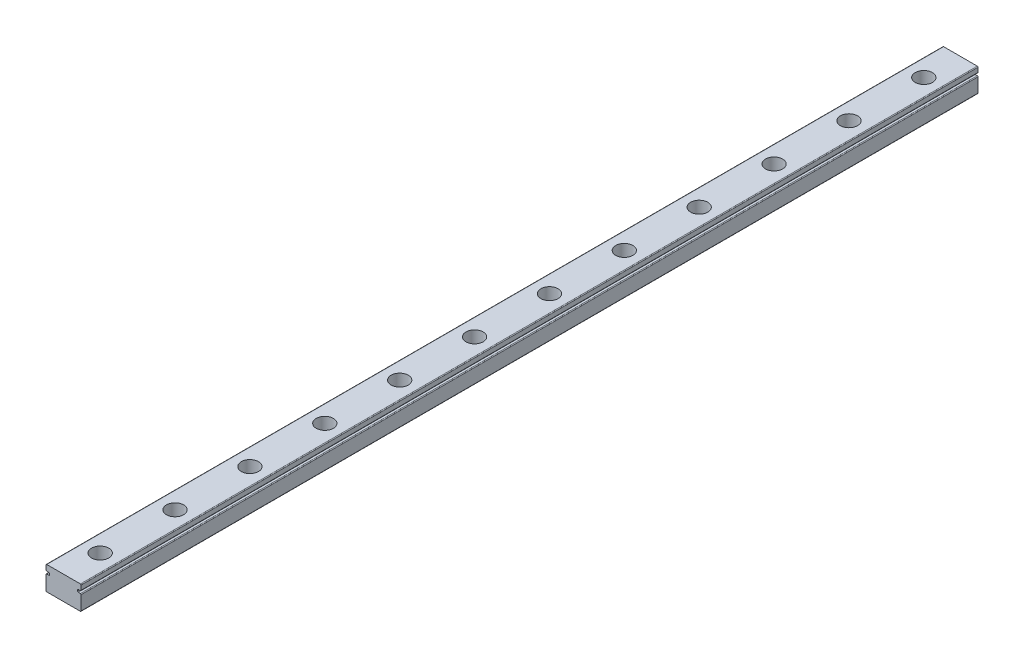
SolidWorks part; units mm, degrees
ref_plane "Front Plane" through (0, 0, 0) normal (0, 0, 1) x (1, 0, 0)
ref_plane "Top Plane" through (0, 0, 0) normal (0, 1, 0) x (1, 0, 0)
ref_plane "Right Plane" through (0, 0, 0) normal (1, 0, 0) x (0, 0, -1)
sketch "Sketch1" plane through (0, 0, 0) normal (0, 0, 1) x (1, 0, 0)
  line L0 (-5.715, 2.0574) -> (-5.0419, 2.0574)
  line L1 (-5.715, 4.0386) -> (5.715, 4.0386)
  line L2 (-5.969, 3.7846) -> (-5.969, 2.3114)
  line L3 (-5.715, -4.0386) -> (5.715, -4.0386)
  line L4 (5.969, 3.7846) -> (5.969, 2.3114)
  line L5 (-5.969, 4.0386) -> (5.969, -4.0386) construction
  line L6 (-5.969, -4.0386) -> (5.969, 4.0386) construction
  line L7 (-4.7879, 1.8034) -> (-4.7879, 1.4732)
  line L8 (-5.0419, 1.2192) -> (-5.715, 1.2192)
  line L9 (0, 4.0386) -> (0, -4.0386) construction
  line L10 (5.0419, 1.2192) -> (5.715, 1.2192)
  line L11 (4.7879, 1.8034) -> (4.7879, 1.4732)
  line L12 (5.715, 2.0574) -> (5.0419, 2.0574)
  line L13 (-5.969, 0.9652) -> (-5.969, -3.7846)
  line L14 (5.969, 0.9652) -> (5.969, -3.7846)
  arc A0 (5.715, -4.0386) -> (5.969, -3.7846) centre (5.715, -3.7846) ccw
  arc A1 (5.715, 1.2192) -> (5.969, 0.9652) centre (5.715, 0.9652) cw
  arc A2 (5.715, 4.0386) -> (5.969, 3.7846) centre (5.715, 3.7846) cw
  arc A3 (5.715, 2.0574) -> (5.969, 2.3114) centre (5.715, 2.3114) ccw
  arc A4 (4.7879, 1.8034) -> (5.0419, 2.0574) centre (5.0419, 1.8034) cw
  arc A5 (5.0419, 1.2192) -> (4.7879, 1.4732) centre (5.0419, 1.4732) cw
  arc A6 (-5.0419, 2.0574) -> (-4.7879, 1.8034) centre (-5.0419, 1.8034) cw
  arc A7 (-5.969, -3.7846) -> (-5.715, -4.0386) centre (-5.715, -3.7846) ccw
  arc A8 (-5.715, 1.2192) -> (-5.969, 0.9652) centre (-5.715, 0.9652) ccw
  arc A9 (-4.7879, 1.4732) -> (-5.0419, 1.2192) centre (-5.0419, 1.4732) cw
  arc A10 (-5.715, 2.0574) -> (-5.969, 2.3114) centre (-5.715, 2.3114) cw
  arc A11 (-5.715, 4.0386) -> (-5.969, 3.7846) centre (-5.715, 3.7846) ccw
  point P0 (0, 0)
  point P21 (5.969, 1.2192)
  point P27 (5.969, 2.0574)
  point P30 (4.7879, 2.0574)
  point P33 (4.7879, 1.2192)
  point P36 (-4.7879, 2.0574)
  point P42 (-5.969, 1.2192)
  point P45 (-4.7879, 1.2192)
  point P48 (-5.969, 2.0574)
  dimension "D6" = 0.254
  dimension "D7" = 0.254
  dimension "D1" = 11.938
  dimension "D2" = 8.0772
  dimension "D3" = 0.8382
  dimension "D4" = 9.5758
  dimension "D5" = 1.9812
extrude "Boss-Extrude1" add sketch "Sketch1" along normal mid plane 304.8
sketch "Sketch2" plane through (0, 4.0386, 0) normal (0, 1, 0) x (1, 0, 0)
  line L0 (5.715, 152.4) -> (-5.715, 152.4) construction
  line L2 (5.715, -152.4) -> (-5.715, -152.4) construction
  circle A0 centre (0, 139.954) radius 2.921
  circle A1 centre (0, 114.5078) radius 2.921
  circle A2 centre (0, 89.0616) radius 2.921
  circle A3 centre (0, 63.6155) radius 2.921
  circle A4 centre (0, 38.1693) radius 2.921
  circle A5 centre (0, 12.7231) radius 2.921
  circle A6 centre (0, -12.7231) radius 2.921
  circle A7 centre (0, -38.1693) radius 2.921
  circle A8 centre (0, -63.6155) radius 2.921
  circle A9 centre (0, -89.0616) radius 2.921
  circle A10 centre (0, -114.5078) radius 2.921
  circle A11 centre (0, -139.954) radius 2.921
  point P2 (0, 142.875)
  point P6 (0, 152.4)
  point P30 (0, -142.875)
  dimension "D1" = 5.842
  dimension "D4" = 9.525
  dimension "D2" = 9.525
  dimension "D3" = 12
extrude "Cut-Extrude1" cut sketch "Sketch2" against normal blind 4.699
sketch "Sketch4" plane through (0, -0.6604, 0) normal (0, 1, 0) x (1, 0, 0)
  circle A131 centre (0, 38.1693) radius 1.905
  circle A132 centre (0, 38.1693) radius 2.921
  circle A133 centre (0, 38.1693) radius 2.921 construction
  circle A134 centre (0, 63.6155) radius 2.921
  circle A135 centre (0, 63.6155) radius 2.921 construction
  circle A136 centre (0, 89.0616) radius 2.921
  circle A137 centre (0, 89.0616) radius 2.921 construction
  circle A138 centre (0, 114.5078) radius 2.921
  circle A139 centre (0, 114.5078) radius 2.921 construction
  circle A140 centre (0, 139.954) radius 2.921
  circle A141 centre (0, 139.954) radius 2.921 construction
  circle A142 centre (0, -139.954) radius 2.921
  circle A143 centre (0, -139.954) radius 2.921 construction
  circle A144 centre (0, -114.5078) radius 2.921
  circle A145 centre (0, -114.5078) radius 2.921 construction
  circle A146 centre (0, -89.0616) radius 2.921
  circle A147 centre (0, -89.0616) radius 2.921 construction
  circle A148 centre (0, -63.6155) radius 2.921
  circle A149 centre (0, -63.6155) radius 2.921 construction
  circle A150 centre (0, -38.1693) radius 2.921
  circle A151 centre (0, -38.1693) radius 2.921 construction
  circle A152 centre (0, -12.7231) radius 2.921
  circle A153 centre (0, -12.7231) radius 2.921 construction
  circle A154 centre (0, 12.7231) radius 2.921
  circle A155 centre (0, 12.7231) radius 2.921 construction
  circle A156 centre (0, 63.6155) radius 1.905
  circle A157 centre (0, 89.0616) radius 1.905
  circle A158 centre (0, 114.5078) radius 1.905
  circle A159 centre (0, 139.954) radius 1.905
  circle A160 centre (0, -139.954) radius 1.905
  circle A161 centre (0, -114.5078) radius 1.905
  circle A162 centre (0, -89.0616) radius 1.905
  circle A163 centre (0, -63.6155) radius 1.905
  circle A164 centre (0, -38.1693) radius 1.905
  circle A165 centre (0, -12.7231) radius 1.905
  circle A166 centre (0, 12.7231) radius 1.905
  dimension "D1" = 0
  dimension "D2" = 0
  dimension "D3" = 0
  dimension "D4" = 0
  dimension "D5" = 0
  dimension "D6" = 0
  dimension "D7" = 0
  dimension "D8" = 0
  dimension "D9" = 0
  dimension "D10" = 0
  dimension "D11" = 0
  dimension "D12" = 0
  dimension "D13" = 1.016
extrude "Cut-Extrude2" cut sketch "Sketch4" against normal through all
